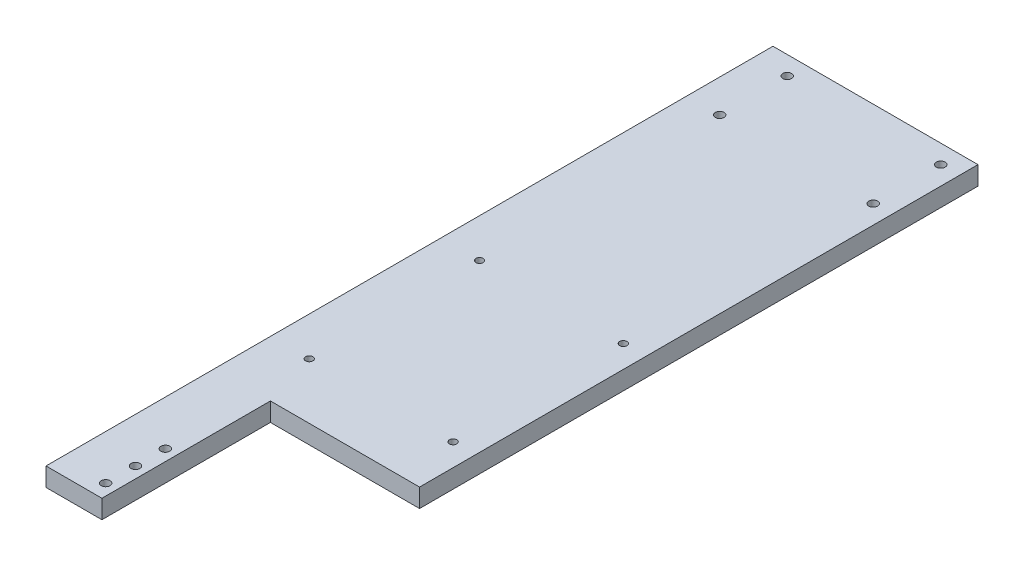
SolidWorks part; units mm, degrees
material "Acrylic (Medium-high impact)"
ref_plane "Front Plane" through (0, 0, 0) normal (0, 0, 1) x (1, 0, 0)
ref_plane "Top Plane" through (0, 0, 0) normal (0, 1, 0) x (1, 0, 0)
ref_plane "Right Plane" through (0, 0, 0) normal (1, 0, 0) x (0, 0, -1)
sketch "Sketch1" plane through (0, 0, 0) normal (0, 1, 0) x (1, 0, 0)
  line L1 (0, 0) -> (69.85, 0)
  line L2 (0, 0) -> (0, 247.65)
  line L3 (0, 247.65) -> (69.85, 247.65)
  line L4 (69.85, 0) -> (69.85, 247.65)
  dimension "D1" = 69.85
  dimension "D2" = 247.65
extrude "Boss-Extrude1" add sketch "Sketch1" along normal blind 6.35
sketch "Sketch2" plane through (0, 6.35, 0) normal (0, 1, 0) x (1, 0, 0)
  line L1 (69.85, 0) -> (19.05, 0)
  line L2 (69.85, 0) -> (69.85, 57.404)
  line L3 (69.85, 57.404) -> (19.05, 57.404)
  line L4 (19.05, 0) -> (19.05, 57.404)
  dimension "D1" = 50.8
  dimension "D2" = 57.404
extrude "Cut-Extrude1" cut sketch "Sketch2" against normal through all
sketch "Sketch3" plane through (0, 6.35, 0) normal (0, 1, 0) x (1, 0, 0)
  line L0 (15.24, 5.08) -> (15.24, 25.4) construction
  line L1 (0, 0) -> (19.05, 0) construction
  line L2 (19.05, 57.404) -> (19.05, 0) construction
  circle A0 centre (15.24, 5.08) radius 1.5
  circle A1 centre (15.24, 25.4) radius 1.5
  circle A2 centre (15.24, 15.24) radius 1.5
  dimension "D1" = 3
  dimension "D2" = 20.32
  dimension "D3" = 5.08
  dimension "D4" = 3.81
extrude "Cut-Extrude2" cut sketch "Sketch3" against normal through all
sketch "Sketch4" plane through (0, 6.35, 0) normal (0, 1, 0) x (1, 0, 0)
  line L0 (69.85, 57.404) -> (69.85, 247.65) construction
  line L1 (11.2, 218.3) -> (63.5, 218.3) construction
  line L2 (11.2, 218.3) -> (11.2, 241.3) construction
  line L3 (11.2, 241.3) -> (63.5, 241.3) construction
  line L4 (63.5, 218.3) -> (63.5, 241.3) construction
  line L5 (69.85, 247.65) -> (0, 247.65) construction
  circle A0 centre (63.5, 241.3) radius 1.5
  circle A1 centre (63.5, 218.3) radius 1.5
  circle A2 centre (11.2, 218.3) radius 1.5
  circle A3 centre (11.2, 241.3) radius 1.5
  dimension "D3" = 3
  dimension "D1" = 52.3
  dimension "D2" = 23
  dimension "D4" = 6.35
  dimension "D5" = 6.35
extrude "Cut-Extrude3" cut sketch "Sketch4" against normal through all
sketch "Sketch5" plane through (0, 6.35, 0) normal (0, 1, 0) x (1, 0, 0)
  line L0 (69.85, 57.404) -> (69.85, 247.65) construction
  line L1 (62.23, 76.454) -> (13.23, 76.454) construction
  line L2 (62.23, 76.454) -> (62.23, 134.454) construction
  line L3 (62.23, 134.454) -> (13.23, 134.454) construction
  line L4 (13.23, 76.454) -> (13.23, 134.454) construction
  line L5 (69.85, 57.404) -> (19.05, 57.404) construction
  circle A0 centre (13.23, 134.454) radius 1.25
  circle A1 centre (62.23, 134.454) radius 1.25
  circle A2 centre (62.23, 76.454) radius 1.25
  circle A3 centre (13.23, 76.454) radius 1.25
  dimension "D3" = 2.5
  dimension "D1" = 49
  dimension "D2" = 58
  dimension "D4" = 7.62
  dimension "D5" = 19.05
extrude "Cut-Extrude4" cut sketch "Sketch5" against normal through all
